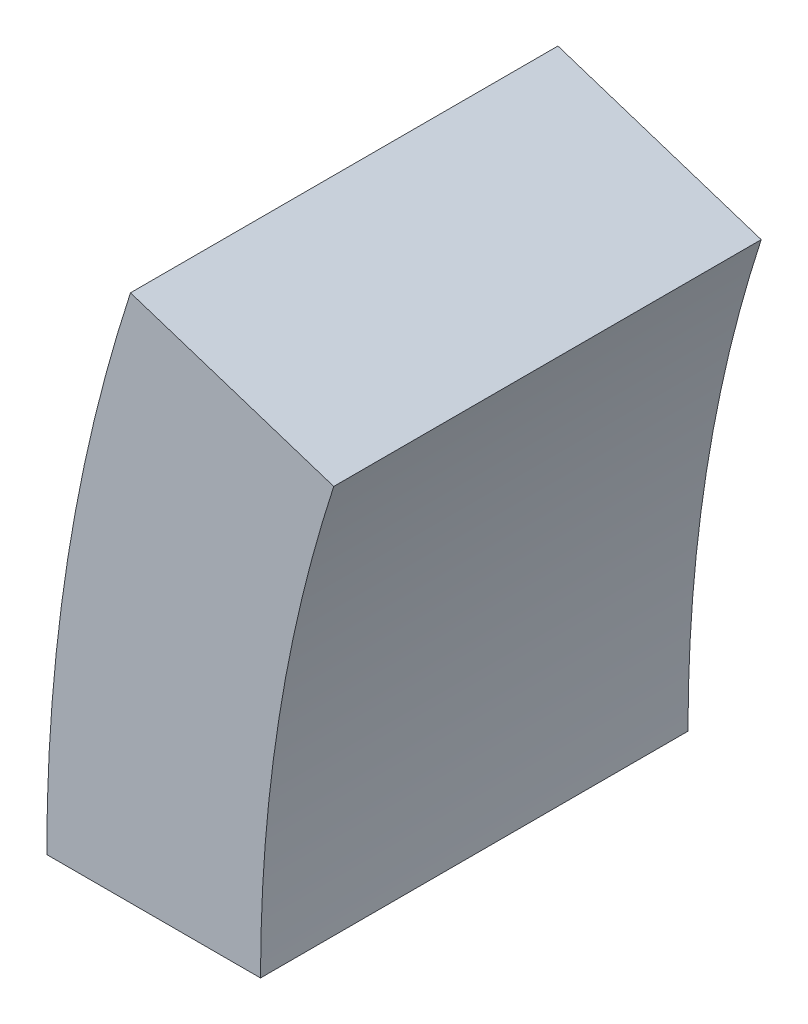
SolidWorks part; units mm, degrees
material "砖"
ref_plane "前视基准面" through (0, 0, 0) normal (0, 0, 1) x (1, 0, 0)
ref_plane "上视基准面" through (0, 0, 0) normal (0, 1, 0) x (1, 0, 0)
ref_plane "右视基准面" through (0, 0, 0) normal (1, 0, 0) x (0, 0, -1)
sketch "草图1" plane through (0, 0, 0) normal (0, 0, 1) x (1, 0, 0)
  line L0 (-4560, 0) -> (-7920, 0)
  line L1 (-12480, 7680) -> (0, 7680)
  line L2 (-12480, 7680) -> (-12480, 0)
  line L3 (-12480, 0) -> (0, 0)
  line L4 (0, 7680) -> (0, 0)
  line L5 (-7920, 0) -> (-7920, 3840)
  line L6 (-7920, 3840) -> (-4560, 3840)
  line L7 (-4560, 3840) -> (-4560, 0)
  line L8 (-7920, 3840) -> (-8160, 3840)
  line L9 (-4560, 3840) -> (-4320, 3840)
  line L10 (-7837.7749, 4359.1486) -> (-8066.0285, 4433.3126)
  line L11 (-7599.1486, 4827.4792) -> (-7793.3126, 4968.5477)
  line L12 (-7227.4792, 5199.1486) -> (-7368.5477, 5393.3126)
  line L13 (-6759.1486, 5437.7749) -> (-6833.3126, 5666.0285)
  line L14 (-6240, 5520) -> (-6240, 5760)
  line L15 (-5720.8514, 5437.7749) -> (-5646.6874, 5666.0285)
  line L16 (-5252.5208, 5199.1486) -> (-5111.4523, 5393.3126)
  line L17 (-4880.8514, 4827.4792) -> (-4686.6874, 4968.5477)
  line L18 (-4642.2251, 4359.1486) -> (-4413.9715, 4433.3126)
  line L19 (-4560, 3840) -> (-4320, 3840)
  line L20 (-4573.7633, 3298.6069) -> (-4560, 3294.1349)
  line L21 (-6833.3126, 5666.0285) -> (-6928.8298, 5960)
  line L22 (-5683.7694, 5551.9017) -> (-5551.1702, 5960)
  line L23 (-5551.1702, 5960) -> (-6928.8298, 5960)
  line L24 (-7920, 0) -> (-9123.3069, 0)
  line L25 (-8160, 0) -> (-8640, 0)
  line L26 (-8160, 0) -> (-8640, 0)
  line L27 (-8640, 3840) -> (-8160, 3840)
  line L28 (-8640, 3840) -> (-8640, 4264)
  line L29 (-7837.7749, 3320.8514) -> (-7920, 3294.1349) [skipped]
  line L30 (-7599.1486, 2852.5208) -> (-7793.3126, 2711.4523) [skipped]
  line L31 (-7227.4792, 2480.8514) -> (-7368.5477, 2286.6874) [skipped]
  line L32 (-6759.1486, 2242.2251) -> (-6833.3126, 2013.9715) [skipped]
  line L33 (-6240, 2160) -> (-6240, 1920) [skipped]
  line L34 (-5720.8514, 2242.2251) -> (-5646.6874, 2013.9715) [skipped]
  line L35 (-5252.5208, 2480.8514) -> (-5111.4523, 2286.6874) [skipped]
  line L36 (-4880.8514, 2852.5208) -> (-4686.6874, 2711.4523) [skipped]
  line L37 (-8640, 4264) -> (-8112.5982, 4264)
  line L38 (-8112.5982, 4264) -> (-8592.5982, 4264)
  line L39 (-8592.5982, 4264) -> (-8592.5982, 4688)
  line L40 (-8592.5982, 4688) -> (-7962.5841, 4688)
  line L41 (-7962.5841, 4688) -> (-8442.5841, 4688)
  line L42 (-8442.5841, 4688) -> (-8442.5841, 5112)
  line L43 (-8442.5841, 5112) -> (-7678.1989, 5112)
  line L44 (-7678.1989, 5112) -> (-8158.1989, 5112)
  line L45 (-8158.1989, 5112) -> (-8158.1989, 5536)
  line L46 (-8158.1989, 5536) -> (-7139.9911, 5536)
  line L47 (-7139.9911, 5536) -> (-7619.9911, 5536)
  line L48 (-7619.9911, 5536) -> (-7619.9911, 5960)
  line L49 (-7619.9911, 5960) -> (-6928.8298, 5960)
  arc A0 (-4560, 3840) -> (-7920, 3840) centre (-6240, 3840) ccw
  arc A1 (-4320, 3840) -> (-8160, 3840) centre (-6240, 3840) ccw
  point P7 (-6240, 0)
  point P56 (-6240, 3840)
  dimension "D5" = 3840
  dimension "D1" = 12480
  dimension "D2" = 7680
  dimension "D3" = 3360
  dimension "D4" = 3840
  dimension "D7" = 240
  dimension "D8" = 480
  dimension "D9" = 424
  dimension "D10" = 720
  dimension "D11" = 480
  dimension "D12" = 480
  dimension "D13" = 480
  dimension "D14" = 480
  dimension "D6" = 20
extrude "凸台-拉伸1" add sketch "草图1" along normal blind 480 contours L10 A1 L8 A0
scale "缩放比例1" scale about origin uniform scaling yes scale factor 1.3
